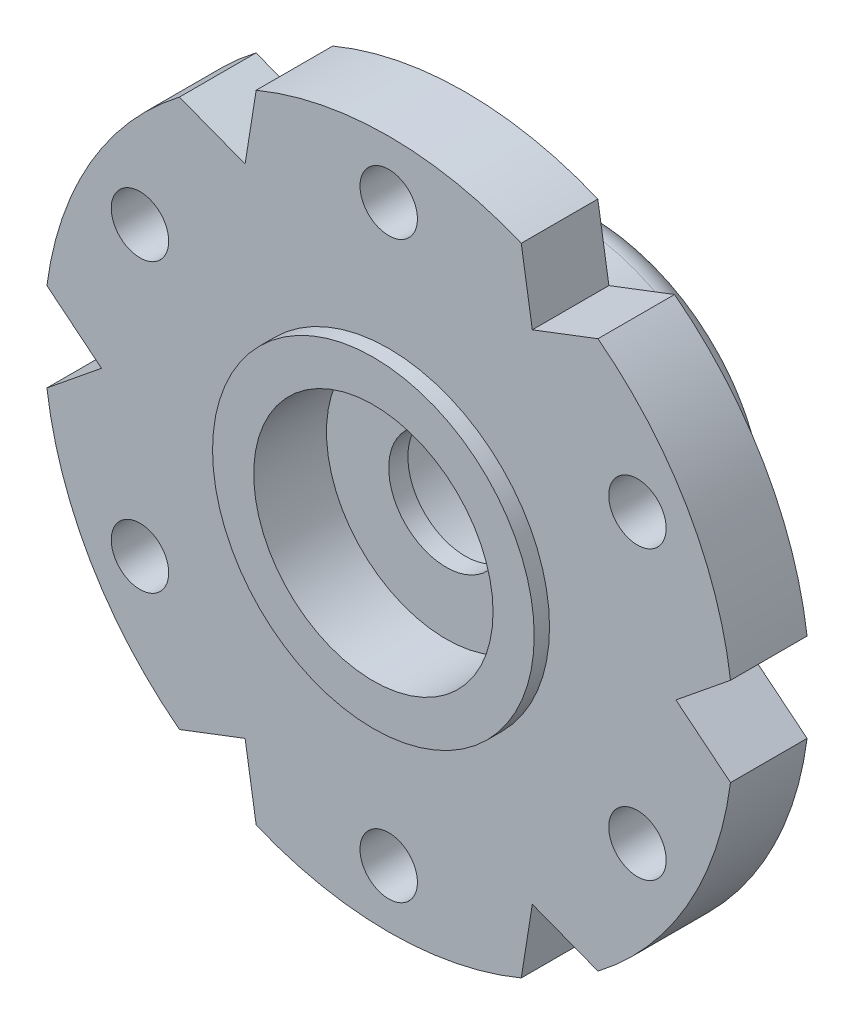
SolidWorks part; units mm, degrees
ref_plane "Front" through (0, 0, 0) normal (0, 0, 1) x (1, 0, 0)
ref_plane "Top" through (0, 0, 0) normal (0, 1, 0) x (1, 0, 0)
ref_plane "Right" through (0, 0, 0) normal (1, 0, 0) x (0, 0, -1)
sketch "Sketch1" plane through (0, 0, 0) normal (0, 0, 1) x (1, 0, 0)
  line L0 (0, 0) -> (0, 16.1) construction
  line L2 (-1.3182, 2.3323) -> (0, 0) construction
  line L3 (-2.5676, 13.9095) -> (-3.75, 6.4952)
  line L4 (0, 0) -> (-7.0771, 0) construction
  line L5 (2.5676, 13.9095) -> (3.75, 6.4952)
  line L6 (13.3297, 4.7312) -> (7.5, 0)
  line L7 (10.7622, 9.1783) -> (3.75, 6.4952)
  line L8 (10.7622, -9.1783) -> (3.75, -6.4952)
  line L9 (13.3297, -4.7312) -> (7.5, 0)
  line L10 (-2.5676, -13.9095) -> (-3.75, -6.4952)
  line L11 (2.5676, -13.9095) -> (3.75, -6.4952)
  line L12 (-13.3297, -4.7312) -> (-7.5, 0)
  line L13 (-10.7622, -9.1783) -> (-3.75, -6.4952)
  line L14 (-10.7622, 9.1783) -> (-3.75, 6.4952)
  line L15 (-13.3297, 4.7312) -> (-7.5, 0)
  circle A0 centre (0, 0) radius 1.5
  arc A1 (2.5676, 13.9095) -> (-2.5676, 13.9095) centre (0, 13.5) ccw
  circle A2 centre (0, 13.5) radius 0.75
  circle A3 centre (0, 10.5) radius 0.75
  circle A4 centre (0, 7.5) radius 0.75
  arc A5 (13.3297, 4.7312) -> (10.7622, 9.1783) centre (11.6913, 6.75) ccw
  circle A6 centre (6.4952, 3.75) radius 0.75
  circle A7 centre (9.0933, 5.25) radius 0.75
  circle A8 centre (11.6913, 6.75) radius 0.75
  arc A9 (10.7622, -9.1783) -> (13.3297, -4.7312) centre (11.6913, -6.75) ccw
  circle A10 centre (6.4952, -3.75) radius 0.75
  circle A11 centre (9.0933, -5.25) radius 0.75
  circle A12 centre (11.6913, -6.75) radius 0.75
  arc A13 (-2.5676, -13.9095) -> (2.5676, -13.9095) centre (0, -13.5) ccw
  circle A14 centre (0, -7.5) radius 0.75
  circle A15 centre (0, -10.5) radius 0.75
  circle A16 centre (0, -13.5) radius 0.75
  arc A17 (-13.3297, -4.7312) -> (-10.7622, -9.1783) centre (-11.6913, -6.75) ccw
  circle A18 centre (-6.4952, -3.75) radius 0.75
  circle A19 centre (-9.0933, -5.25) radius 0.75
  circle A20 centre (-11.6913, -6.75) radius 0.75
  arc A21 (-10.7622, 9.1783) -> (-13.3297, 4.7312) centre (-11.6913, 6.75) ccw
  circle A22 centre (-6.4952, 3.75) radius 0.75
  circle A23 centre (-9.0933, 5.25) radius 0.75
  circle A24 centre (-11.6913, 6.75) radius 0.75
  point P69 (0, 0)
  dimension "D1" = 3
  dimension "D2" = 1.5
  dimension "D7" = 2.6
  dimension "D3" = 15
  dimension "D4" = 21
  dimension "D5" = 27
  dimension "D6" = 6
  dimension "D8" = 7.5
  dimension "D9" = 32.2
extrude "Boss-Extrude1" add sketch "Sketch1" along normal blind 2
sketch "Sketch2" plane through (0, 0, 0) normal (0, 0, -1) x (-1, 0, 0)
  circle A0 centre (0, 0) radius 4.75
  circle A1 centre (0, 0) radius 2.7
  dimension "D1" = 9.5
  dimension "D2" = 5.4
extrude "Boss-Extrude2" add sketch "Sketch2" along normal blind 3.5
sketch "Sketch3" plane through (0, 0, 2) normal (0, 0, 1) x (1, 0, 0)
  circle A0 centre (0, 0) radius 4.2
  circle A1 centre (0, 0) radius 3.125
  dimension "D1" = 8.4
  dimension "D2" = 6.25
extrude "Boss-Extrude3" add sketch "Sketch3" along normal blind 0.4
sketch "Sketch4" plane through (0, 0, 2) normal (0, 0, 1) x (1, 0, 0)
  circle A1 centre (0, 0) radius 3.125
  circle A2 centre (0, 0) radius 3.125
  dimension "D1" = 0
extrude "Cut-Extrude1" cut sketch "Sketch4" against normal blind 1.5
fillet "Fillet1" radius 0.75 2 edges at (-4.75, 0, -3.5) (4.75, 0, 0)
sketch "Sketch5" plane through (0, 0, 2) normal (0, 0, 1) x (1, 0, 0)
  circle A0 centre (0, 0) radius 9
  dimension "D1" = 18
extrude "Cut-Extrude2" cut sketch "Sketch5" against normal through all flip side to cut
